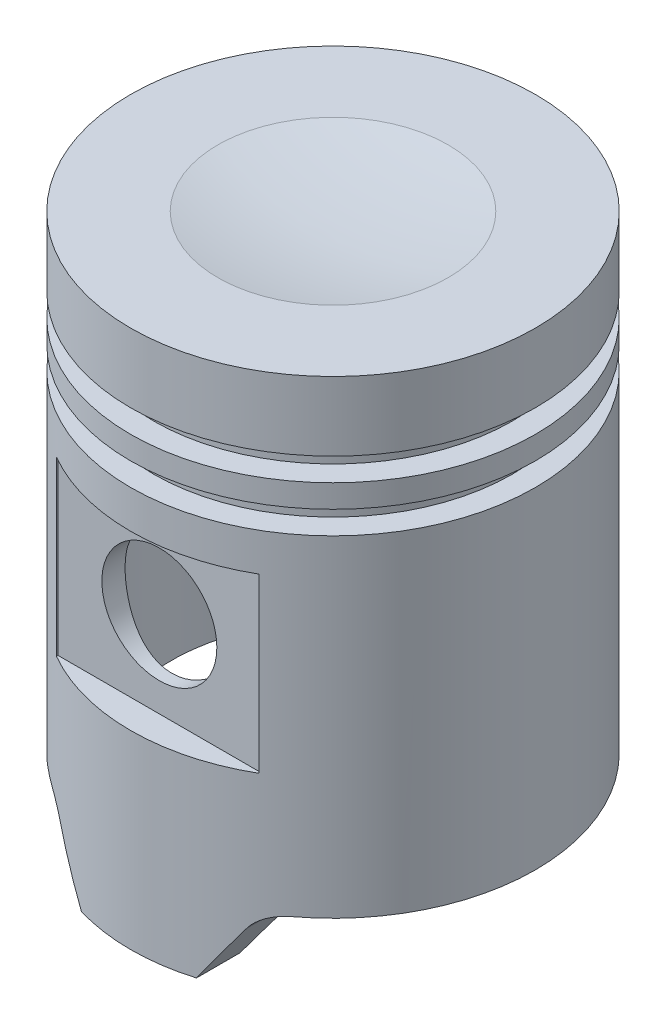
SolidWorks part; units mm, degrees
ref_plane "Front Plane" through (0, 0, 0) normal (0, 0, 1) x (1, 0, 0)
ref_plane "Top Plane" through (0, 0, 0) normal (0, 1, 0) x (1, 0, 0)
ref_plane "Right Plane" through (0, 0, 0) normal (1, 0, 0) x (0, 0, -1)
sketch "Sketch1" plane through (0, 0, 0) normal (0, 0, 1) x (1, 0, 0)
  line L0 (0, 0) -> (0, 58.166)
  line L1 (12.7127, 59.436) -> (22.352, 59.436)
  line L2 (22.352, 59.436) -> (22.352, 51.816)
  line L3 (22.352, 51.816) -> (19.812, 51.816)
  line L4 (19.812, 51.816) -> (19.812, 49.276)
  line L5 (19.812, 49.276) -> (22.352, 49.276)
  line L6 (22.352, 49.276) -> (22.352, 46.736)
  line L7 (22.352, 46.736) -> (19.812, 46.736)
  line L8 (19.812, 46.736) -> (19.812, 44.196)
  line L9 (19.812, 44.196) -> (22.352, 44.196)
  line L10 (22.352, 44.196) -> (22.352, 0)
  line L11 (22.352, 0) -> (0, 0)
  arc A0 (0, 58.166) -> (12.7127, 59.436) centre (0, 122.428) ccw
  dimension "D10" = 128.524
  dimension "D2" = 7.62
  dimension "D3" = 2.54
  dimension "D4" = 2.54
  dimension "D5" = 2.54
  dimension "D6" = 2.54
  dimension "D7" = 2.54
  dimension "D8" = 2.54
  dimension "D9" = 2.54
  dimension "D11" = 44.196
  dimension "D12" = 122.428
  dimension "D13" = 22.352
revolve "Revolve2" add sketch "Sketch1" angle 360 about L0
sketch "Sketch3" plane through (0, 0, 0) normal (0, -1, 0) x (-1, 0, 0)
  circle A0 centre (0, 0) radius 17.78
  dimension "D1" = 35.56
extrude "Cut-Extrude2" cut sketch "Sketch3" against normal blind 51.816
sketch "Sketch4" plane through (0, 0, 0) normal (0, 0, 1) x (1, 0, 0)
  circle A0 centre (0, 30.48) radius 6.35
  dimension "D1" = 12.7
  dimension "D2" = 30.48
extrude "Cut-Extrude3" cut sketch "Sketch4" against normal through all both and the other way through all
sketch "Sketch5" plane through (0, 0, 0) normal (0, 0, 1) x (1, 0, 0)
  line L0 (0, 36.83) -> (0, 24.13) construction
  line L1 (-11.176, 40.005) -> (11.176, 40.005)
  line L2 (-11.176, 40.005) -> (-11.176, 20.955)
  line L3 (-11.176, 20.955) -> (11.176, 20.955)
  line L4 (11.176, 40.005) -> (11.176, 20.955)
  line L5 (6.35, 30.48) -> (-6.35, 30.48) construction
  circle A0 centre (0, 30.48) radius 6.35 construction
  circle A1 centre (0, 30.48) radius 6.35 construction
  dimension "D1" = 19.05
  dimension "D2" = 11.176
  dimension "D3" = 22.352
  dimension "D4" = 9.525
extrude "Cut-Extrude5" cut sketch "Sketch5" along normal through all from offset 19.177
mirror "Mirror1" about plane through (0, 0, 0) normal (0, 0, 1) of "Cut-Extrude5"
sketch "Sketch6" plane through (0, 0, 0) normal (0, 0, 1) x (1, 0, 0)
  line L0 (22.352, 7.62) -> (13.4705, 7.62)
  line L1 (22.352, 0) -> (22.352, 44.196) construction
  line L2 (10.3008, 5.924) -> (6.35, 0)
  line L3 (-22.352, 0) -> (22.352, 0) construction
  line L4 (22.352, 7.62) -> (22.352, 0)
  line L5 (6.35, 0) -> (22.352, 0)
  arc A0 (13.4705, 7.62) -> (10.3008, 5.924) centre (13.4705, 3.81) ccw
  dimension "D4" = 3.81
  dimension "D1" = 7.62
  dimension "D2" = 16.002
  dimension "D3" = 236.3
extrude "Cut-Extrude6" cut sketch "Sketch6" against normal through all both and the other way through all
mirror "Mirror2" about plane through (0, 0, 0) normal (1, 0, 0) of "Cut-Extrude6"
